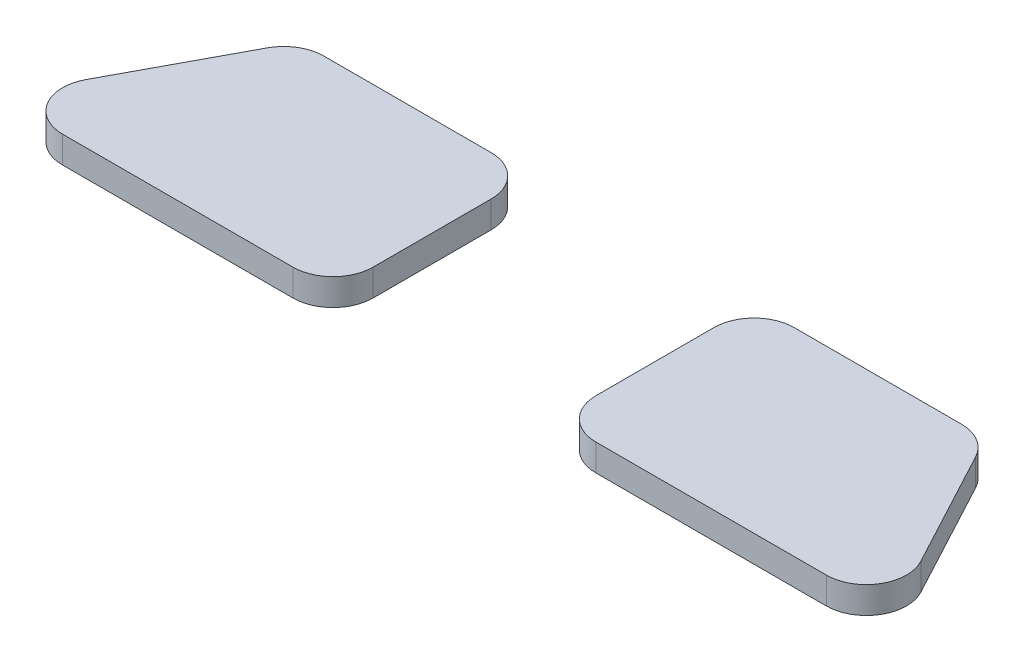
SolidWorks part; units mm, degrees
ref_plane "前视基准面" through (0, 0, 0) normal (0, 0, 1) x (1, 0, 0)
ref_plane "上视基准面" through (0, 0, 0) normal (0, 1, 0) x (1, 0, 0)
ref_plane "右视基准面" through (0, 0, 0) normal (1, 0, 0) x (0, 0, -1)
other "Configuration Table"
sketch "草图1" plane through (0, 0, 0) normal (0, 1, 0) x (1, 0, 0)
  line L0 (1.7977, 0) -> (14.29, 0)
  line L1 (17.29, -3) -> (17.29, -11.81)
  line L2 (14.29, -14.81) -> (-2.9136, -14.81)
  line L3 (-0.8478, -1.5853) -> (-5.5591, -10.3953)
  line L4 (25.6099, 8.5554) -> (25.6099, -22.2942) construction
  line L5 (33.9298, -3) -> (33.9298, -11.81)
  line L6 (36.9298, -14.81) -> (54.1334, -14.81)
  line L7 (52.0675, -1.5853) -> (56.7789, -10.3953)
  line L8 (49.4221, 0) -> (36.9298, 0)
  arc A0 (-2.9136, -14.81) -> (-5.5591, -10.3953) centre (-2.9136, -11.81) cw
  arc A1 (17.29, -11.81) -> (14.29, -14.81) centre (14.29, -11.81) cw
  arc A2 (14.29, 0) -> (17.29, -3) centre (14.29, -3) cw
  arc A3 (1.7977, 0) -> (-0.8478, -1.5853) centre (1.7977, -3) ccw
  arc A4 (36.9298, 0) -> (33.9298, -3) centre (36.9298, -3) ccw
  arc A5 (33.9298, -11.81) -> (36.9298, -14.81) centre (36.9298, -11.81) ccw
  arc A6 (54.1334, -14.81) -> (56.7789, -10.3953) centre (54.1334, -11.81) ccw
  arc A7 (49.4221, 0) -> (52.0675, -1.5853) centre (49.4221, -3) cw
  point P7 (-7.92, -14.81)
  point P10 (17.29, -14.81)
  point P13 (17.29, 0)
  point P16 (0, 0)
  dimension "D4" = 3
  dimension "D1" = 17.29
  dimension "D2" = 14.81
  dimension "D3" = 25.21
extrude "凸台-拉伸1" add sketch "草图1" along normal blind 2
